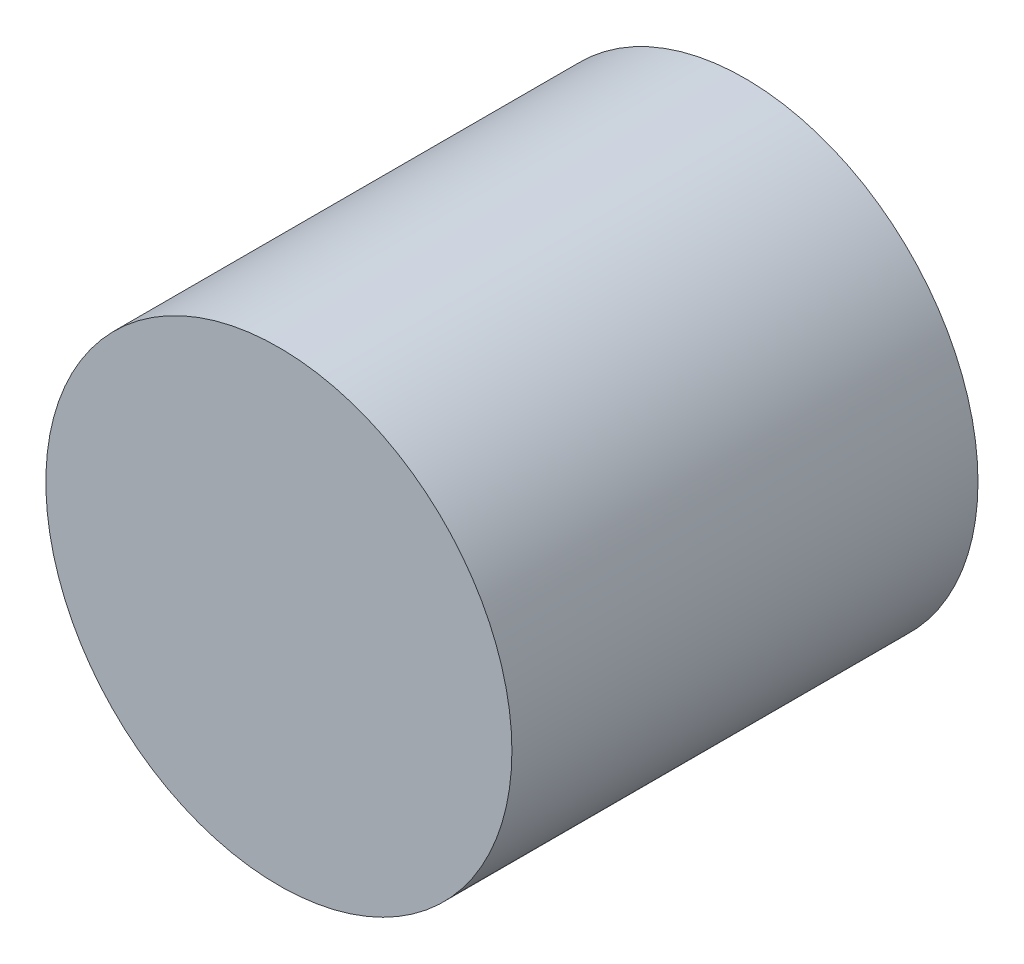
SolidWorks part; units mm, degrees
material "Reines Gold"
ref_plane "Ebene vorne" through (0, 0, 0) normal (0, 0, 1) x (1, 0, 0)
ref_plane "Ebene oben" through (0, 0, 0) normal (0, 1, 0) x (1, 0, 0)
ref_plane "Ebene rechts" through (0, 0, 0) normal (1, 0, 0) x (0, 0, -1)
sketch "Skizze1" plane through (0, 0, 0) normal (0, 0, 1) x (1, 0, 0)
  circle A0 centre (0, 0) radius 7.5
  dimension "D1" = 15
extrude "Aufsatz-Linear austragen1" add sketch "Skizze1" along normal mid plane 15
